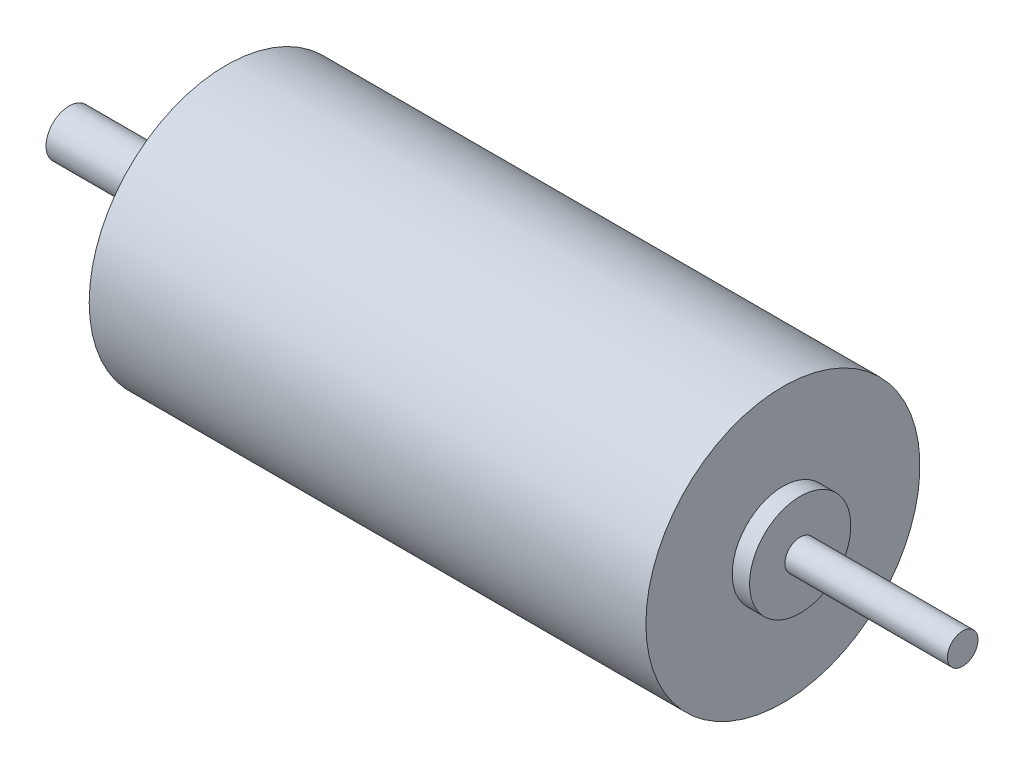
SolidWorks part; units mm, degrees
ref_plane "Front Plane" through (0, 0, 0) normal (0, 0, 1) x (1, 0, 0)
ref_plane "Top Plane" through (0, 0, 0) normal (0, 1, 0) x (1, 0, 0)
ref_plane "Right Plane" through (0, 0, 0) normal (1, 0, 0) x (0, 0, -1)
sketch "Sketch1" plane through (0, 0, 0) normal (0, 0, 1) x (1, 0, 0)
  line L0 (-106.4586, 10.313) -> (-106.4586, 13.263)
  line L1 (-106.4586, 13.263) -> (-88.6586, 13.263)
  line L2 (-106.4586, 10.313) -> (7.3414, 10.313) construction
  line L3 (-106.4586, 10.313) -> (7.3414, 10.313)
  line L4 (-88.6586, 13.263) -> (-88.6586, 16.763)
  line L5 (-88.6586, 16.763) -> (-86.4586, 16.763)
  line L6 (-86.4586, 16.763) -> (-86.4586, 27.763)
  line L7 (-86.4586, 27.763) -> (-15.5586, 27.763)
  line L8 (-15.5586, 27.763) -> (-15.5586, 16.763)
  line L11 (-15.5586, 16.763) -> (-13.3586, 16.763)
  line L12 (-13.3586, 16.763) -> (-13.3586, 12.263)
  line L15 (-13.3586, 12.263) -> (7.3414, 12.263)
  line L16 (7.3414, 12.263) -> (7.3414, 10.313)
revolve "Revolve1" add sketch "Sketch1" angle 360 about L2
